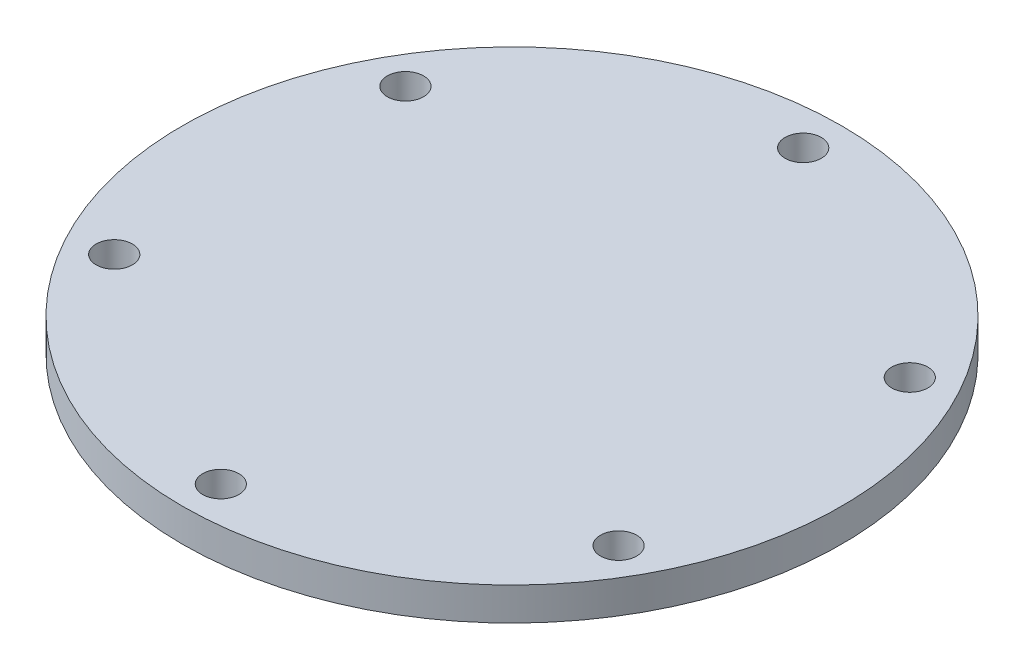
SolidWorks part; units mm, degrees
ref_plane "Alzado" through (0, 0, 0) normal (0, 0, 1) x (1, 0, 0)
ref_plane "Planta" through (0, 0, 0) normal (0, 1, 0) x (1, 0, 0)
ref_plane "Vista lateral" through (0, 0, 0) normal (1, 0, 0) x (0, 0, -1)
sketch "Croquis1" plane through (0, 0, 0) normal (0, 1, 0) x (1, 0, 0)
  circle A0 centre (0, 0) radius 50
  circle A1 centre (0, 0) radius 44 construction
  circle A2 centre (0, 44.178) radius 2.5 construction
  dimension "D1" = 100
  dimension "D2" = 5
  dimension "D3" = 6
extrude "Saliente-Extruir1" add sketch "Croquis1" along normal blind 5 contours A0
hole_wizard "Taladro de margen para M51" positions "Croquis3" profile "Croquis2" hole size "M5" standard "ISO" end condition through all
sketch "Croquis3" plane through (0, 0, 0) normal (0, -1, 0) x (-1, 0, 0)
  point P0 (0, 44.178)
sketch "Croquis2" plane through (0, 0, -44.178) normal (1, 0, 0) x (0, 0, -1)
  line L0 (0, 0) -> (0, 5)
  line L1 (0, 5) -> (2.75, 5)
  line L2 (2.75, 5) -> (2.75, 0)
  line L5 (2.75, 0) -> (0, 0)
  line L11 (0, -6.35) -> (0, 107.95) construction
  dimension "Diámetro de taladro hasta el siguiente" = 5.5
  dimension "Profundidad de taladro hasta el siguiente" = 5
pattern_circular "MatrizC1" count 6 over 360 about axis through (0, 0, 0) along (0, 1, 0) of "Taladro de margen para M51"
